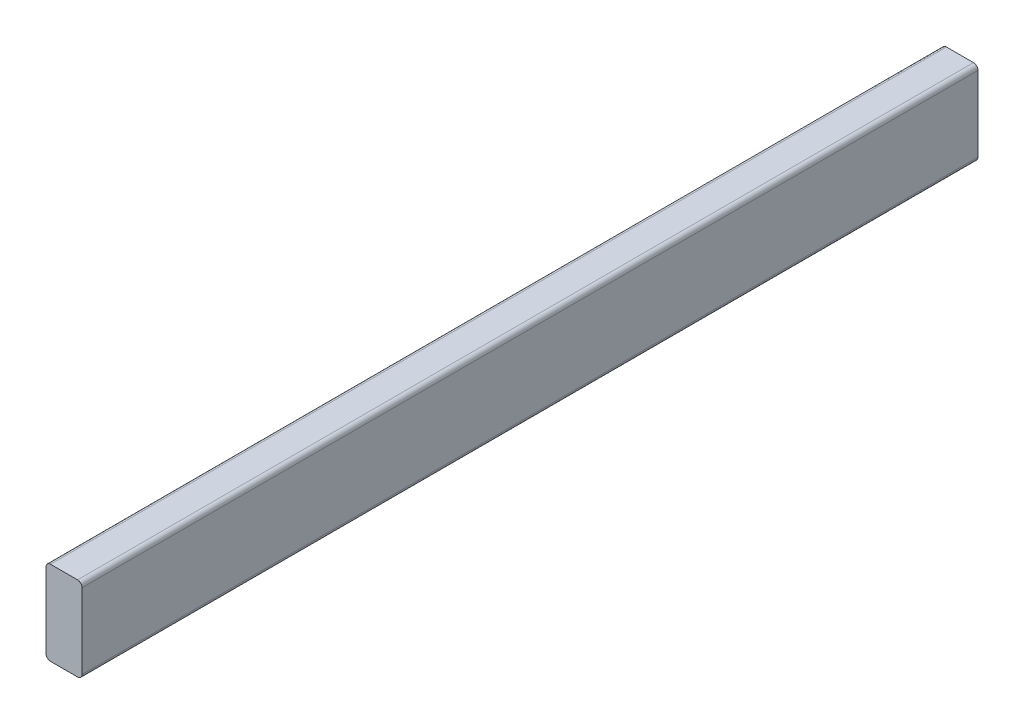
SolidWorks part; units mm, degrees
material "Pine"
ref_plane "Front Plane" through (0, 0, 0) normal (0, 0, 1) x (1, 0, 0)
ref_plane "Top Plane" through (0, 0, 0) normal (0, 1, 0) x (1, 0, 0)
ref_plane "Right Plane" through (0, 0, 0) normal (1, 0, 0) x (0, 0, -1)
sketch "Sketch1" plane through (0, 0, 0) normal (0, 0, 1) x (1, 0, 0)
  line L0 (-819.8306, 88.9) -> (-819.8306, 304.7381) construction
  line L1 (-781.7306, 88.9) -> (-819.8306, 88.9)
  line L2 (-781.7306, 88.9) -> (-781.7306, 0)
  line L3 (-781.7306, 0) -> (-819.8306, 0)
  line L4 (-819.8306, 88.9) -> (-819.8306, 0)
  line L5 (-781.7306, 0) -> (-831.7368, 0) construction
extrude "Boss-Extrude1" add sketch "Sketch1" against normal up to surface (946.6588 mm away)
fillet "Fillet1" radius 4.7625 4 edges at (-819.8306, 0, -473.3294) (-781.7306, 0, -473.3294) (-819.8306, 88.9, -473.3294) (-781.7306, 88.9, -473.3294)
